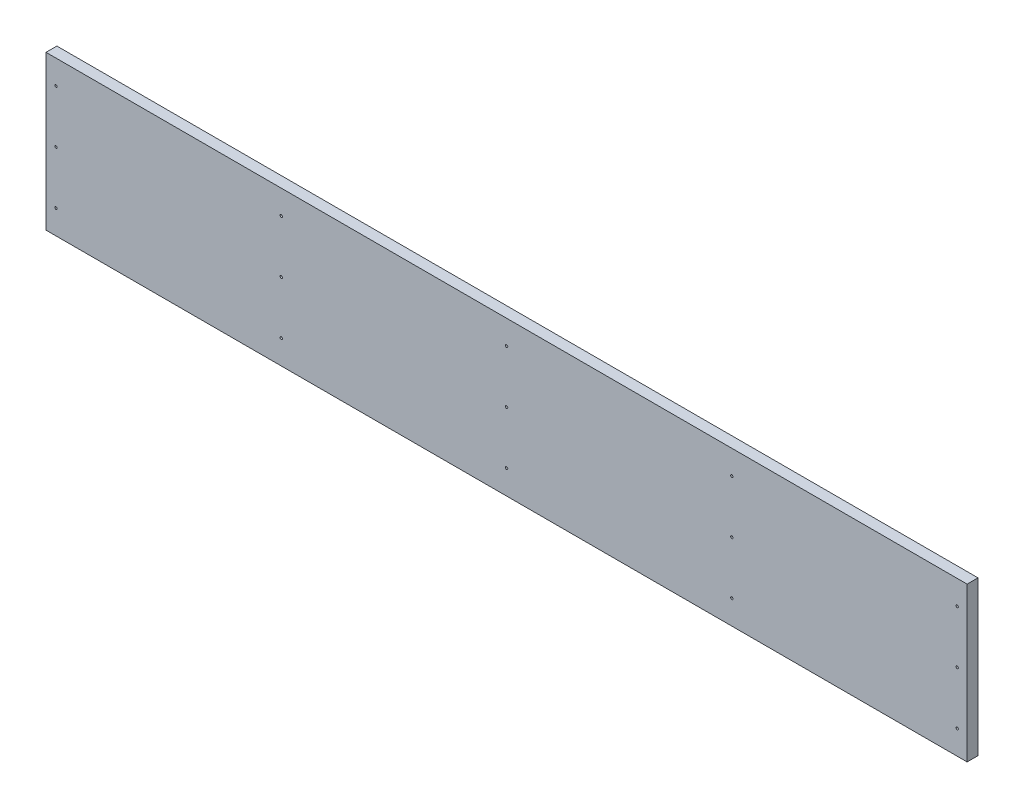
SolidWorks part; units mm, degrees
ref_plane "Ebene vorne" through (0, 0, 0) normal (0, 0, 1) x (1, 0, 0)
ref_plane "Ebene oben" through (0, 0, 0) normal (0, 1, 0) x (1, 0, 0)
ref_plane "Ebene rechts" through (0, 0, 0) normal (1, 0, 0) x (0, 0, -1)
sketch "Skizze1" plane through (0, 0, 0) normal (0, 0, 1) x (1, 0, 0)
  line L1 (-762.5, 127.5) -> (762.5, 127.5)
  line L2 (-762.5, 127.5) -> (-762.5, -127.5)
  line L3 (-762.5, -127.5) -> (762.5, -127.5)
  line L4 (762.5, 127.5) -> (762.5, -127.5)
  line L5 (-762.5, 127.5) -> (762.5, -127.5) construction
  line L6 (-762.5, -127.5) -> (762.5, 127.5) construction
  point P0 (0, 0)
  dimension "D1" = 255
  dimension "D2" = 1525
extrude "Aufsatz-Linear austragen1" add sketch "Skizze1" along normal blind 18
sketch "Skizze3" plane through (0, 0, 18) normal (0, 0, 1) x (1, 0, 0)
  line L0 (-762.5, 127.5) -> (-762.5, -127.5) construction
  line L1 (762.5, 127.5) -> (-762.5, 127.5) construction
  circle A0 centre (-746, 87.5) radius 2
  circle A1 centre (-746, 0) radius 2
  circle A2 centre (-746, -87.5) radius 2
  circle A3 centre (-373, -87.5) radius 2
  circle A4 centre (-373, 0) radius 2
  circle A5 centre (-373, 87.5) radius 2
  circle A6 centre (0, -87.5) radius 2
  circle A7 centre (0, 0) radius 2
  circle A8 centre (0, 87.5) radius 2
  circle A9 centre (373, -87.5) radius 2
  circle A10 centre (373, 0) radius 2
  circle A11 centre (373, 87.5) radius 2
  circle A12 centre (746, -87.5) radius 2
  circle A13 centre (746, 0) radius 2
  circle A14 centre (746, 87.5) radius 2
  dimension "D1" = 4
  dimension "D8" = 4
  dimension "D9" = 4
  dimension "D2" = 16.5
  dimension "D3" = 16.5
  dimension "D4" = 16.5
  dimension "D5" = 40
  dimension "D6" = 87.5
  dimension "D7" = 87.5
  dimension "D10" = 5
extrude "Schnitt-Linear austragen1" cut sketch "Skizze3" against normal up to next
